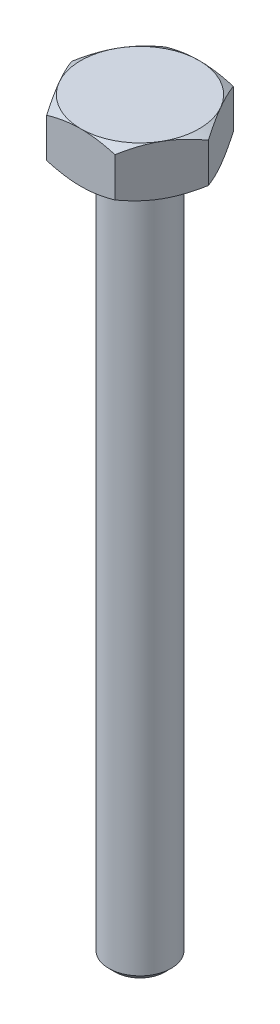
SolidWorks part; units mm, degrees
ref_plane "Alzado" through (0, 0, 0) normal (0, 0, 1) x (1, 0, 0)
ref_plane "Planta" through (0, 0, 0) normal (0, 1, 0) x (1, 0, 0)
ref_plane "Vista lateral" through (0, 0, 0) normal (1, 0, 0) x (0, 0, -1)
sketch "Croquis1" plane through (0, 0, 0) normal (0, 1, 0) x (1, 0, 0)
  line L1 (10.9697, 0) -> (5.4848, 9.5)
  line L2 (5.4848, 9.5) -> (-5.4848, 9.5)
  line L3 (-5.4848, 9.5) -> (-10.9697, 0)
  line L4 (-10.9697, 0) -> (-5.4848, -9.5)
  line L5 (-5.4848, -9.5) -> (5.4848, -9.5)
  line L6 (5.4848, -9.5) -> (10.9697, 0)
  circle A0 centre (0, 0) radius 9.5 construction
  dimension "D1" = 19
extrude "Saliente-Extruir1" add sketch "Croquis1" along normal blind 8
sketch "Croquis2" plane through (0, 8, 0) normal (0, 1, 0) x (1, 0, 0)
  circle A0 centre (0, 0) radius 4.25
  point P3 (0, 0)
  dimension "D1" = 8.5
extrude "Cortar-Extruir1" cut sketch "Croquis2" against normal through all
sketch "Croquis3" plane through (0, 8, 0) normal (0, 1, 0) x (1, 0, 0)
  circle A0 centre (0, 0) radius 9.5
  point P3 (0, 0)
  dimension "19" = 19
extrude "Cortar-Extruir2" cut sketch "Croquis3" against normal blind 8 draft 60 flip side to cut
sketch "Croquis4" plane through (0, 0, 0) normal (0, -1, 0) x (1, 0, 0)
  circle A0 centre (0, 0) radius 9.5
  dimension "D1" = 19
extrude "Cortar-Extruir3" cut sketch "Croquis4" against normal blind 8 draft 60 flip side to cut
sketch "Croquis5" plane through (0, 8, 0) normal (0, 1, 0) x (1, 0, 0)
  circle A0 centre (0, 0) radius 5
  dimension "D1" = 10
extrude "Saliente-Extruir3" add sketch "Croquis5" against normal blind 120
chamfer "Chaflán2" distance 1 angle 45 1 edges at (0, -112, 5)
